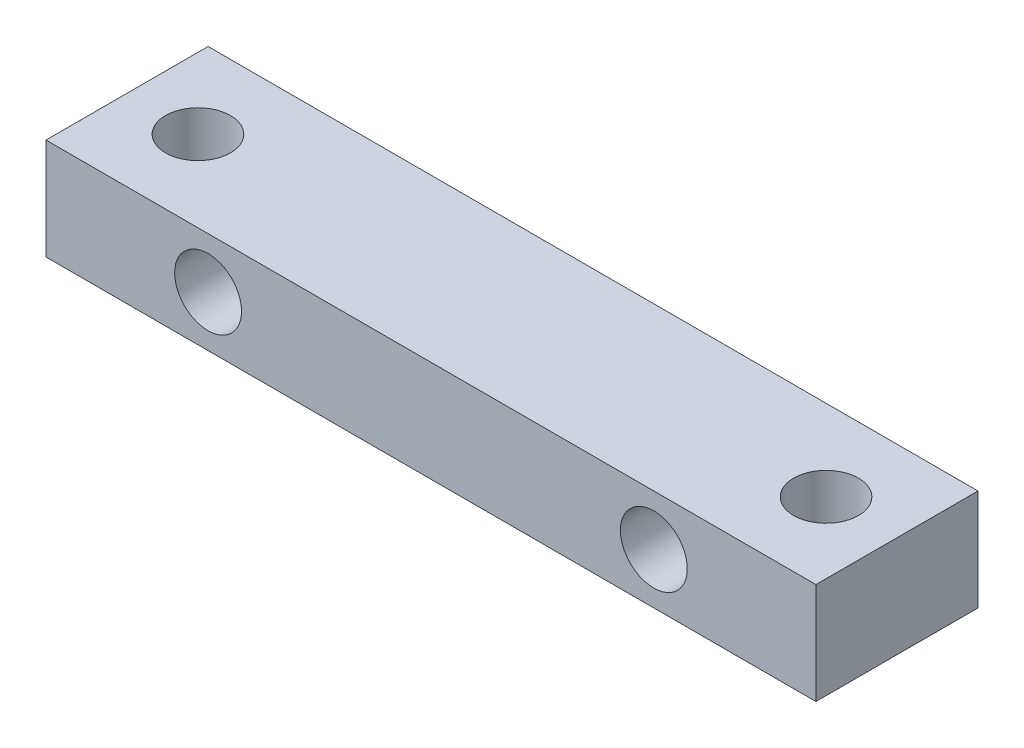
SolidWorks part; units mm, degrees
material "acero"
ref_plane "Alzado" through (0, 0, 0) normal (0, 0, 1) x (1, 0, 0)
ref_plane "Planta" through (0, 0, 0) normal (0, 1, 0) x (1, 0, 0)
ref_plane "Vista lateral" through (0, 0, 0) normal (1, 0, 0) x (0, 0, -1)
sketch "Croquis1" plane through (0, 0, 0) normal (0, 0, 1) x (1, 0, 0)
  line L1 (0, 0) -> (38, 0)
  line L2 (0, 0) -> (0, 5)
  line L3 (0, 5) -> (38, 5)
  line L4 (38, 0) -> (38, 5)
  dimension "D1" = 38
  dimension "D2" = 5
extrude "Saliente-Extruir1" add sketch "Croquis1" along normal blind 8
hole_wizard "Diámetro de taladro Ø3.2 (3.2)1" positions "Croquis3D1" profile "Croquis2" hole size "Ø3.2" standard "Iso"
sketch3d "Croquis3D1"
  line L0 (0, 5, 4) -> (38, 5, 4) construction
  line L1 (0, 5, 8) -> (0, 5, 0) construction
  line L2 (38, 5, 8) -> (38, 5, 0) construction
  point P0 (3.5, 5, 4)
  point P2 (34.5, 5, 4)
  dimension "D1" = 3.5
  dimension "D2" = 3.5
sketch "Croquis2" plane through (3.5, 5, 4) normal (1, 0, 0) x (0, 0, 1)
  line L0 (0, 0) -> (0, 12.9614)
  line L1 (0, 12.9614) -> (1.6, 12)
  line L2 (1.6, 12) -> (1.6, 0)
  line L5 (1.6, 0) -> (0, 0)
  line L10 (0, 12.9614) -> (-1.6, 12) construction
  line L11 (0, -6.35) -> (0, 107.95) construction
  dimension "Diámetro de taladro" = 3.2
  dimension "Profundidad de taladro" = 12
  dimension "Ángulo de perforador" = 118
hole_wizard "Taladro roscado M41" positions "Croquis3D2" profile "Croquis3" tap size "M4" standard "ISO" end condition up to next
sketch3d "Croquis3D2"
  line L0 (0, 2.5, 0) -> (38, 2.5, 0) construction
  line L1 (0, 5, 0) -> (0, 0, 0) construction
  line L2 (38, 0, 0) -> (38, 5, 0) construction
  line L4 (3.5, 5, 4) -> (3.5, 5, 0) construction
  line L6 (38, 5, 0) -> (0, 5, 0) construction
  line L7 (8, 2.5, 0) -> (8, 5, 0) construction
  line L8 (8, 5, 0) -> (3.5, 5, 0) construction
  line L10 (30, 2.5, 0) -> (30, 5, 0) construction
  line L14 (34.5, 0, 4) -> (34.5, 5, 4) construction
  line L16 (34.5, 5, 4) -> (34.5, 5, 0) construction
  circle A0 centre (3.5, 5, 4) radius 1.6 construction
  point P0 (8, 2.5, 0)
  point P2 (30, 2.5, 0)
  point P49 (3.5, 6.6, 4)
  dimension "D1" = 4.5
  dimension "D2" = 4.5
sketch "Croquis3" plane through (8, 2.5, 0) normal (1, 0, 0) x (0, 1, 0)
  line L0 (0, 0) -> (0, 8)
  line L1 (0, 8) -> (1.65, 8)
  line L2 (1.65, 8) -> (1.65, 0)
  line L5 (1.65, 0) -> (0, 0)
  line L11 (0, -6.35) -> (0, 107.95) construction
  dimension "Diámetro de perforador para roscar hasta el siguiente" = 3.3
  dimension "Profundidad de perforador para roscar hasta el siguiente" = 8
cosmetic thread "Rosca de taladro3" parameters "D2"=4
cosmetic thread "Rosca de taladro4" parameters "D2"=4
